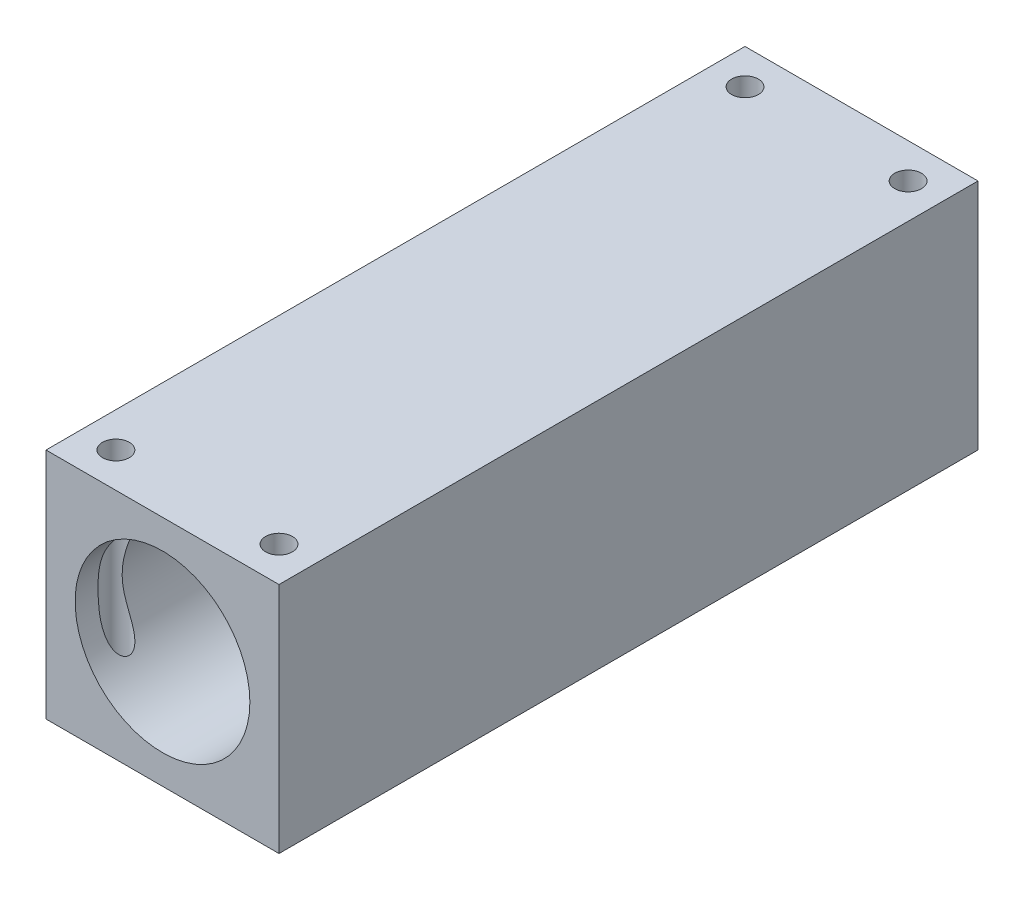
SolidWorks part; units mm, degrees
material "1060 Alloy"
ref_plane "Front Plane" through (0, 0, 0) normal (0, 0, 1) x (1, 0, 0)
ref_plane "Top Plane" through (0, 0, 0) normal (0, 1, 0) x (1, 0, 0)
ref_plane "Right Plane" through (0, 0, 0) normal (1, 0, 0) x (0, 0, -1)
sketch "Sketch1" plane through (0, 0, 0) normal (0, 0, 1) x (1, 0, 0)
  line L1 (0, 0) -> (20, 0)
  line L2 (0, 0) -> (0, 20)
  line L3 (0, 20) -> (20, 20)
  line L4 (20, 0) -> (20, 20)
  circle A0 centre (10, 10) radius 7.5
  dimension "D1" = 20
  dimension "D3" = 15
  dimension "D2" = 20
  dimension "D4" = 10
  dimension "D5" = 10
extrude "Boss-Extrude1" add sketch "Sketch1" along normal blind 60
sketch "Sketch2" plane through (0, 20, 0) normal (0, 1, 0) x (1, 0, 0)
  line L0 (20, 0) -> (0, 0) construction
  line L1 (20, -60) -> (0, -60) construction
  line L3 (0, -60) -> (0, 0) construction
  line L4 (20, -60) -> (20, 0) construction
  circle A0 centre (3, -57) radius 1.15
  circle A1 centre (17, -57) radius 1.15
  circle A2 centre (3, -3) radius 1.15
  circle A3 centre (17, -3) radius 1.15
  dimension "D1" = 2.3
  dimension "D2" = 3
  dimension "D3" = 3
  dimension "D4" = 3
  dimension "D5" = 3
extrude "Cut-Extrude1" cut sketch "Sketch2" against normal through all
